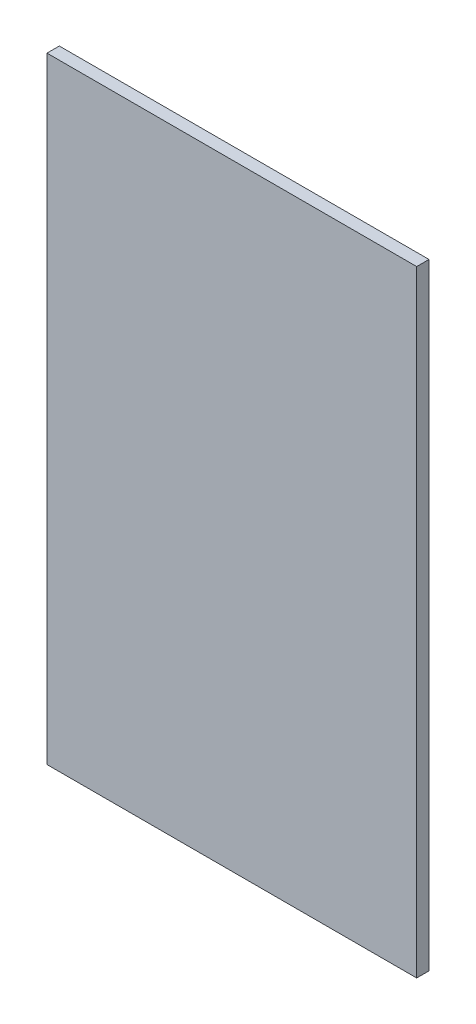
SolidWorks part; units mm, degrees
ref_plane "Front Plane" through (0, 0, 0) normal (0, 0, 1) x (1, 0, 0)
ref_plane "Top Plane" through (0, 0, 0) normal (0, 1, 0) x (1, 0, 0)
ref_plane "Right Plane" through (0, 0, 0) normal (1, 0, 0) x (0, 0, -1)
sketch "Sketch1" plane through (0, 0, 0) normal (0, 0, 1) x (1, 0, 0)
  line L1 (0, 0) -> (300, 0)
  line L2 (0, 0) -> (0, 500)
  line L3 (0, 500) -> (300, 500)
  line L4 (300, 0) -> (300, 500)
  dimension "D1" = 300
  dimension "D2" = 500
extrude "Extrude1" add sketch "Sketch1" along normal blind 10
